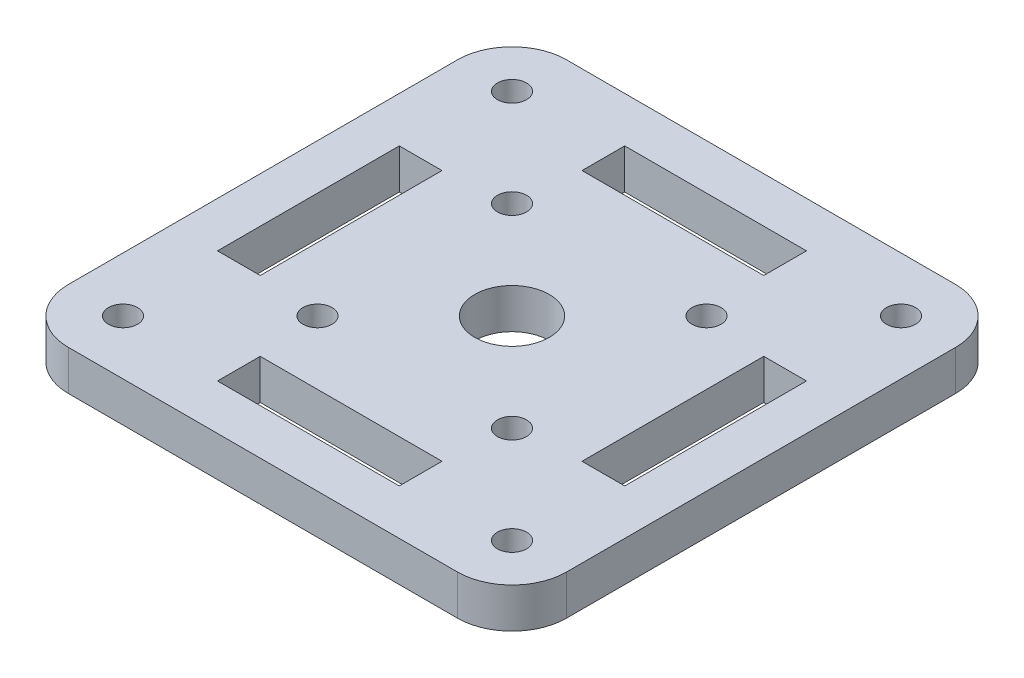
SolidWorks part; units mm, degrees
ref_plane "前视基准面" through (0, 0, 0) normal (0, 0, 1) x (1, 0, 0)
ref_plane "上视基准面" through (0, 0, 0) normal (0, 1, 0) x (1, 0, 0)
ref_plane "右视基准面" through (0, 0, 0) normal (1, 0, 0) x (0, 0, -1)
sketch "草图1" plane through (0, 0, 0) normal (0, 1, 0) x (1, 0, 0)
  line L0 (0, 0) -> (27.4, 27.4) construction
  line L1 (-27.4, 27.4) -> (27.4, 27.4)
  line L2 (-27.4, 27.4) -> (-27.4, -27.4)
  line L3 (-27.4, -27.4) -> (27.4, -27.4)
  line L4 (27.4, 27.4) -> (27.4, -27.4)
  line L5 (0, -27.4) -> (0, 27.4) construction
  line L6 (-27.4, 0) -> (27.4, 0) construction
  line L7 (17.7, -5) -> (17.7, 5)
  line L8 (17.7, 5) -> (22.4, 5) construction
  line L9 (22.4, 5) -> (22.4, -5)
  line L10 (17.7, 5) -> (17.7, 10)
  line L11 (17.7, 10) -> (22.4, 10)
  line L12 (22.4, 10) -> (22.4, 5)
  line L13 (0, 0) -> (27.4, -27.4) construction
  line L14 (22.4, -10) -> (22.4, -5)
  line L15 (17.7, -10) -> (22.4, -10)
  line L16 (17.7, -5) -> (17.7, -10)
  line L17 (17.7, -5) -> (22.4, -5) construction
  line L18 (-5, 17.7) -> (-5, 22.4) construction
  line L19 (5, 17.7) -> (5, 22.4) construction
  line L20 (-5, 17.7) -> (-10, 17.7)
  line L21 (-10, 17.7) -> (-10, 22.4)
  line L22 (-10, 22.4) -> (-5, 22.4)
  line L23 (10, 22.4) -> (5, 22.4)
  line L24 (10, 17.7) -> (10, 22.4)
  line L25 (5, 17.7) -> (10, 17.7)
  line L26 (5, 22.4) -> (-5, 22.4)
  line L27 (-5, 17.7) -> (5, 17.7)
  line L28 (0, 0) -> (-27.4, -27.4) construction
  line L29 (0, 0) -> (-27.4, 27.4) construction
  line L30 (5, -17.7) -> (5, -22.4) construction
  line L31 (-5, -17.7) -> (-5, -22.4) construction
  line L32 (5, -17.7) -> (10, -17.7)
  line L33 (10, -17.7) -> (10, -22.4)
  line L34 (10, -22.4) -> (5, -22.4)
  line L35 (-10, -22.4) -> (-5, -22.4)
  line L36 (-10, -17.7) -> (-10, -22.4)
  line L37 (-5, -17.7) -> (-10, -17.7)
  line L38 (-5, -22.4) -> (5, -22.4)
  line L39 (5, -17.7) -> (-5, -17.7)
  line L40 (-17.7, -5) -> (-22.4, -5) construction
  line L41 (-17.7, 5) -> (-22.4, 5) construction
  line L42 (-17.7, 5) -> (-17.7, -5)
  line L43 (-22.4, -5) -> (-22.4, 5)
  line L44 (-17.7, -5) -> (-17.7, -10)
  line L45 (-17.7, -10) -> (-22.4, -10)
  line L46 (17.7, 10) -> (17.7, 17.7) construction
  line L47 (-22.4, -10) -> (-22.4, -5)
  line L48 (-22.4, 10) -> (-22.4, 5)
  line L49 (-17.7, 10) -> (-22.4, 10)
  line L50 (-17.7, 5) -> (-17.7, 10)
  circle A0 centre (0, 0) radius 4.1
  circle A1 centre (21.4, 21.4) radius 1.6
  circle A2 centre (21.4, -21.4) radius 1.6
  circle A3 centre (-21.4, -21.4) radius 1.6
  circle A4 centre (-21.4, 21.4) radius 1.6
  point P17 (22.4, 0)
  point P18 (17.7, 0)
  point P32 (0, 17.7)
  point P33 (0, 22.4)
  point P42 (0, -17.7)
  point P43 (0, -22.4)
  point P53 (-22.4, 0)
  point P54 (-17.7, 0)
  dimension "D1" = 8.2
  dimension "D8" = 3.2
  dimension "D2" = 45
  dimension "D3" = 4.7
  dimension "D5" = 5
  dimension "D6" = 5
  dimension "D7" = 5
  dimension "D9" = 6
extrude "凸台-拉伸1" add sketch "草图1" along normal blind 4.4
fillet "圆角1" radius 6 4 edges at (-27.4, 2.2, 27.4) (-27.4, 2.2, -27.4) (27.4, 2.2, -27.4) (27.4, 2.2, 27.4)
sketch "草图2" plane through (0, 4.4, 0) normal (0, 1, 0) x (1, 0, 0)
  line L0 (0, 0) -> (21.4, 21.4) construction
  circle A0 centre (10.7, 10.7) radius 1.6
  circle A1 centre (10.7, -10.7) radius 1.6
  circle A2 centre (-10.7, -10.7) radius 1.6
  circle A3 centre (-10.7, 10.7) radius 1.6
  point P15 (0, 0)
  dimension "D1" = 3.2
  dimension "D2" = 4
extrude "切除-拉伸1" cut sketch "草图2" against normal blind 10
